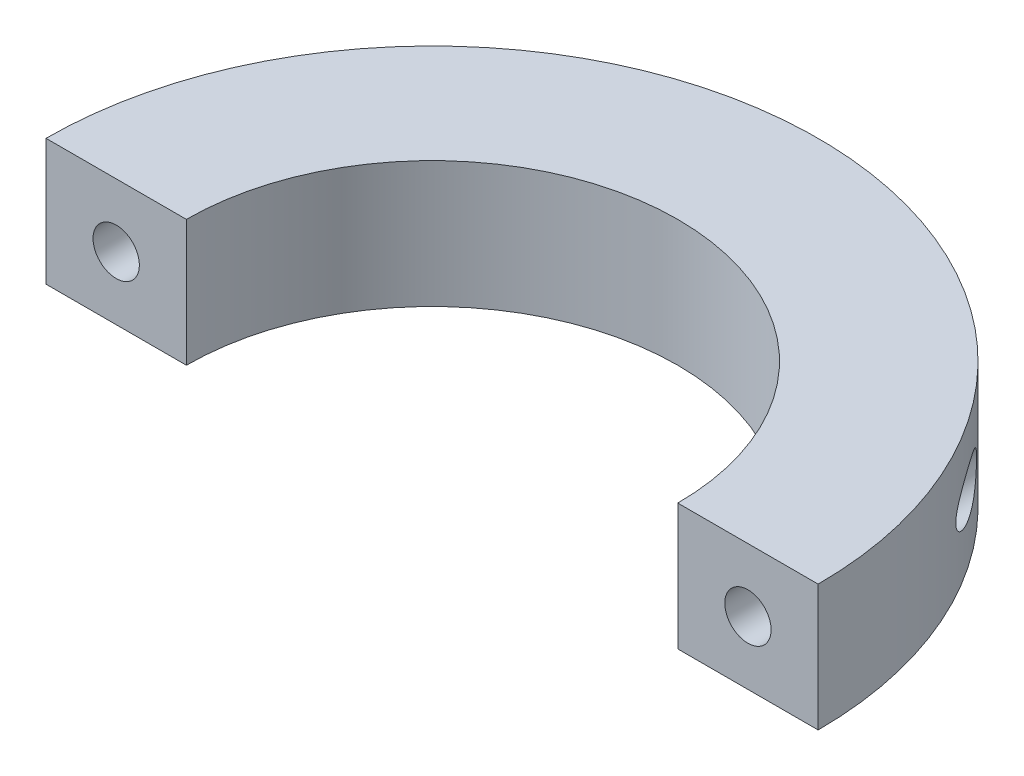
SolidWorks part; units mm, degrees
other "Markup1"
sketch "Sketch14" plane through (50, -13.9925, 0) normal (0.3766, -0.0256, 0.926) x (0.9251, 0.0632, -0.3745)
ref_plane "Front Plane" through (0, 0, 0) normal (0, 0, 1) x (1, 0, 0)
ref_plane "Top Plane" through (0, 0, 0) normal (0, 1, 0) x (1, 0, 0)
ref_plane "Right Plane" through (0, 0, 0) normal (1, 0, 0) x (0, 0, -1)
sketch "Sketch1" plane through (0, 0, 0) normal (0, 1, 0) x (1, 0, 0)
  line L0 (-25.1828, 0) -> (30.5526, 0) construction
  line L1 (-27.5, 0) -> (-17.5, 0)
  line L2 (17.5, 0) -> (27.5, 0)
  arc A0 (27.5, 0) -> (-27.5, 0) centre (0, 0) ccw
  arc A1 (17.5, 0) -> (-17.5, 0) centre (0, 0) ccw
  dimension "D1" = 17.5
  dimension "D2" = 27.5
extrude "Boss-Extrude1" add sketch "Sketch1" along normal mid plane 9
sketch "Sketch2" plane through (0, 0, 0) normal (0, 0, 1) x (1, 0, 0)
  line L0 (0, 10.378) -> (0, -13.9925) construction
  line L1 (17.5, -4.5) -> (27.5, -4.5) construction
  line L2 (-27.5, -4.5) -> (-17.5, -4.5) construction
  point P1 (22.5, 0)
  point P11 (-22.5, 0)
  dimension "D1" = 4.5
  dimension "D3" = 22.5
  dimension "D2" = 22.5
  dimension "D4" = 4.5
sketch "Sketch5" plane through (0, 4.5, 0) normal (0, 1, 0) x (1, 0, 0)
  line L0 (-21.7417, 0) -> (21.6322, 0) construction
  line L1 (-27.5, 0) -> (-17.5, 0) construction
  line L2 (17.5, 0) -> (27.5, 0) construction
  line L3 (-40.5, 0) -> (-40, 0)
  line L4 (40, 0) -> (40.5, 0)
  line L6 (-45.5, 0) -> (-45, 0)
  line L8 (45, 0) -> (45.5, 0)
  arc A0 (40.5, 0) -> (-40.5, 0) centre (0, 0) ccw
  arc A1 (40, 0) -> (-40, 0) centre (0, 0) ccw
  arc A2 (45, 0) -> (-45, 0) centre (0, 0) ccw
  arc A3 (45.5, 0) -> (-45.5, 0) centre (0, 0) ccw
  dimension "D1" = 0.5
  dimension "D3" = 0.5
  dimension "D2" = 40
  dimension "D4" = 45
hole_wizard "Tap Drill for M5x0.8 Tap1" positions "3DSketch2" profile "Sketch11" hole size "M5x0.8" standard "ANSI Metric"
sketch3d "3DSketch2"
  point P0 (-42.5, 0, 0)
  point P3 (42.5, 0, 0)
sketch "Sketch11" plane through (-42.5, 0, 0) normal (1, 0, 0) x (0, -1, 0)
  line L0 (0, 0) -> (0, 50)
  line L1 (0, 50) -> (2.1, 50)
  line L2 (2.1, 50) -> (2.1, 0)
  line L5 (2.1, 0) -> (0, 0)
  line L11 (0, -6.35) -> (0, 107.95) construction
  dimension "Thru Hole Dia." = 4.2
  dimension "Thru Hole Depth" = 50
hole_wizard "Tap Drill for M4x0.7 Tap1" positions "3DSketch1" profile "Sketch6" hole size "M4x0.7" standard "ANSI Metric" end condition through all
sketch3d "3DSketch1"
  point P0 (22.5, 0, 0)
  point P3 (-22.5, 0, 0)
sketch "Sketch6" plane through (22.5, 0, 0) normal (1, 0, 0) x (0, -1, 0)
  line L0 (0, 0) -> (0, 27.5)
  line L1 (0, 27.5) -> (1.65, 27.5)
  line L2 (1.65, 27.5) -> (1.65, 0)
  line L5 (1.65, 0) -> (0, 0)
  line L11 (0, -6.35) -> (0, 107.95) construction
  dimension "Thru Hole Dia." = 3.3
  dimension "Thru Hole Depth" = 27.5
thread "Thread1" pitch 1 start angle 0, offset 0, length 20, pitch 1, diameter 5
ref_plane "Plane1" through (-45, 0, 0) normal (0, -1, 0) x (-1, 0, 0)
sketch "Thread Profile1" plane through (-45, 0, 0) normal (0, -1, 0) x (-1, 0, 0)
  line L0 (0, 0) -> (0, 1) construction
  line L11 (0, 0) -> (0, 0.875)
  line L12 (0, 0.875) -> (-0.5413, 0.5625)
  line L13 (-0.5413, 0.5625) -> (-0.5413, 0.3125)
  line L15 (-0.5413, 0.3125) -> (0, 0)
  line L17 (-0.5413, 0.4375) -> (0, 0.4375) construction
  point P2 (0, 0)
  dimension "Pitch" = 1
  dimension "Profile_Angle" = 60
  dimension "Profile_Land" = 0.25
  dimension "Profile_Height" = 0.5413
thread "Thread2" pitch 1 start angle 0, offset 0, length 20, pitch 1, diameter 5
ref_plane "Plane2" through (40, 0, 0) normal (0, -1, 0) x (-1, 0, 0)
sketch "Thread Profile2" plane through (40, 0, 0) normal (0, -1, 0) x (-1, 0, 0)
  line L0 (0, 0) -> (0, 1) construction
  line L11 (0, 0) -> (0, 0.875)
  line L12 (0, 0.875) -> (-0.5413, 0.5625)
  line L13 (-0.5413, 0.5625) -> (-0.5413, 0.3125)
  line L15 (-0.5413, 0.3125) -> (0, 0)
  line L17 (-0.5413, 0.4375) -> (0, 0.4375) construction
  point P2 (0, 0)
  dimension "Pitch" = 1
  dimension "Profile_Angle" = 60
  dimension "Profile_Land" = 0.25
  dimension "Profile_Height" = 0.5413
